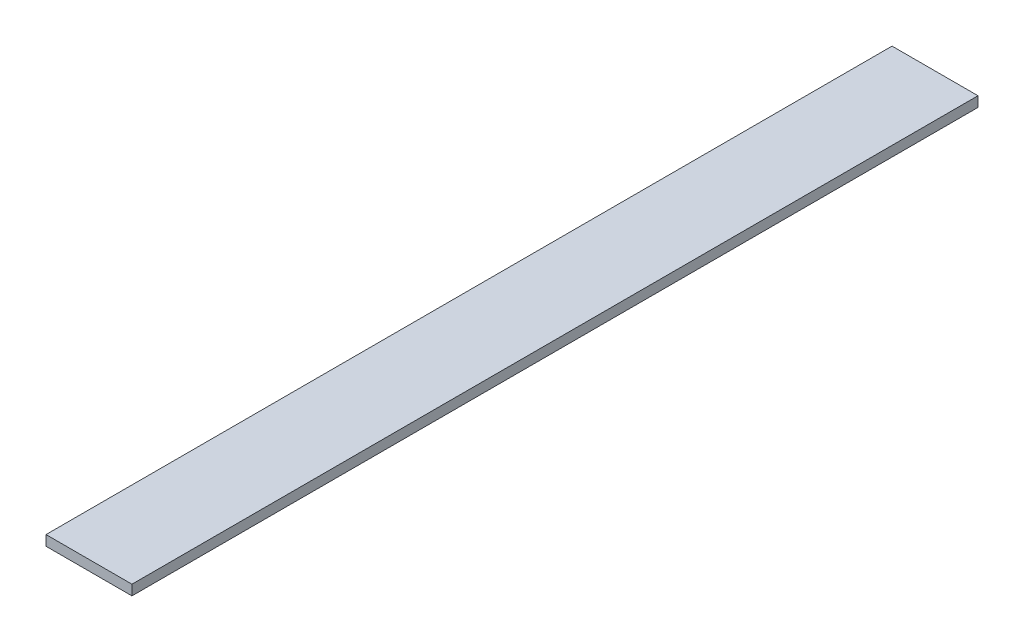
SolidWorks part; units mm, degrees
ref_plane "Alzado" through (0, 0, 0) normal (0, 0, 1) x (1, 0, 0)
ref_plane "Planta" through (0, 0, 0) normal (0, 1, 0) x (1, 0, 0)
ref_plane "Vista lateral" through (0, 0, 0) normal (1, 0, 0) x (0, 0, -1)
sketch "Croquis1" plane through (0, 0, 0) normal (0, 0, 1) x (1, 0, 0)
  line L1 (-25.4, 3) -> (25.4, 3)
  line L2 (-25.4, 3) -> (-25.4, -3)
  line L3 (-25.4, -3) -> (25.4, -3)
  line L4 (25.4, 3) -> (25.4, -3)
  line L5 (-25.4, 3) -> (25.4, -3) construction
  line L6 (-25.4, -3) -> (25.4, 3) construction
  point P0 (0, 0)
  dimension "D1" = 50.8
  dimension "D2" = 6
extrude "Saliente-Extruir1" add sketch "Croquis1" along normal blind 500
